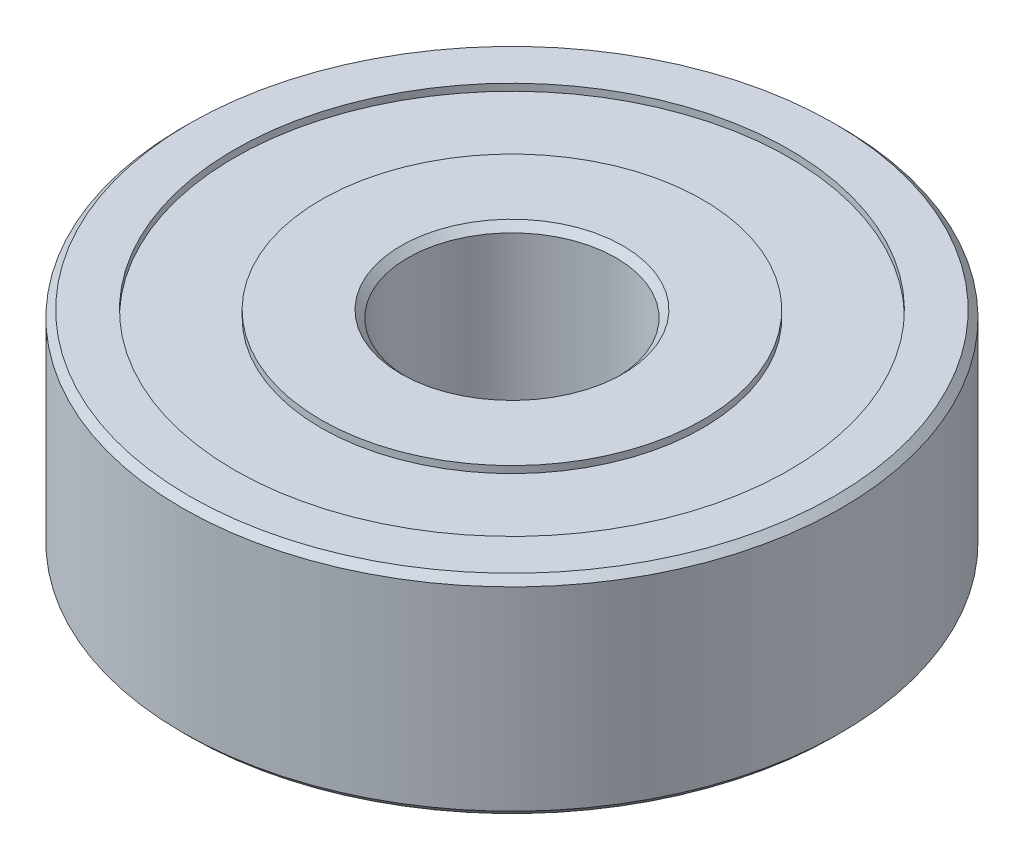
SolidWorks part; units mm, degrees
ref_plane "Front Plane" through (0, 0, 0) normal (0, 0, 1) x (1, 0, 0)
ref_plane "Top Plane" through (0, 0, 0) normal (0, 1, 0) x (1, 0, 0)
ref_plane "Right Plane" through (0, 0, 0) normal (1, 0, 0) x (0, 0, -1)
sketch "Sketch1" plane through (0, 0, 0) normal (0, 1, 0) x (1, 0, 0)
  circle A0 centre (0, 0) radius 9.5
  circle A1 centre (0, 0) radius 3
  dimension "D1" = 19
  dimension "D2" = 6
extrude "Boss-Extrude1" add sketch "Sketch1" along normal blind 6
sketch "Sketch2" plane through (0, 6, 0) normal (0, 1, 0) x (1, 0, 0)
  circle A0 centre (0, 0) radius 5.5
  circle A1 centre (0, 0) radius 8
  dimension "D1" = 16
  dimension "D2" = 11
extrude "Cut-Extrude1" cut sketch "Sketch2" against normal blind 0.2
sketch "Sketch3" plane through (0, 0, 0) normal (0, -1, 0) x (1, 0, 0)
  circle A0 centre (0, 0) radius 5.5 construction
  circle A1 centre (0, 0) radius 8
  circle A2 centre (0, 0) radius 8
  circle A3 centre (0, 0) radius 5.5
  dimension "D1" = 0
extrude "Cut-Extrude2" cut sketch "Sketch3" against normal blind 0.2
chamfer "Chamfer1" distance 0.2 angle 45 4 edges at (0, 6, 9.5) (0, 0, 9.5) (0, 6, 3) (0, 0, 3)
